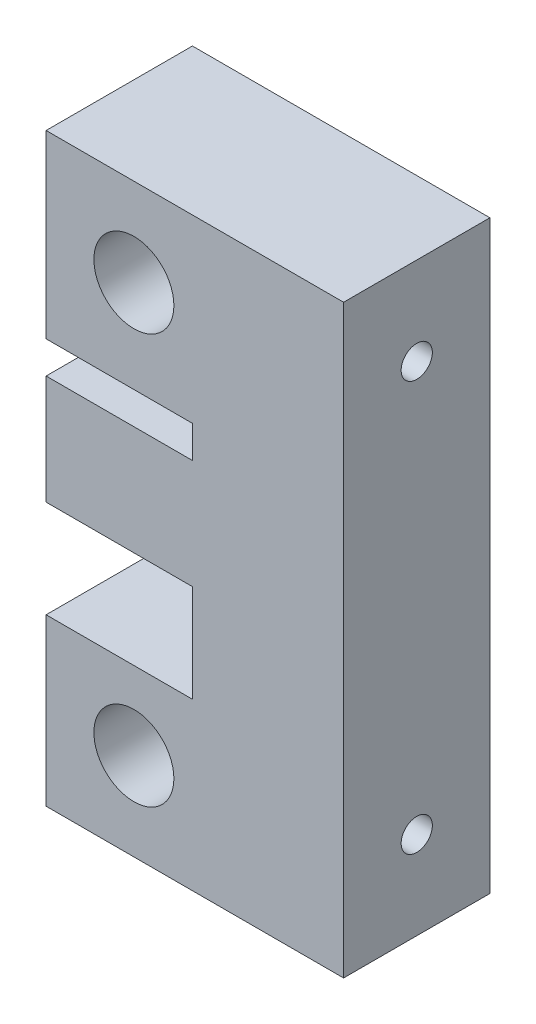
SolidWorks part; units mm, degrees
ref_plane "Front Plane" through (0, 0, 0) normal (0, 0, 1) x (1, 0, 0)
ref_plane "Top Plane" through (0, 0, 0) normal (0, 1, 0) x (1, 0, 0)
ref_plane "Right Plane" through (0, 0, 0) normal (1, 0, 0) x (0, 0, -1)
sketch "Sketch1" plane through (0, 0, 0) normal (0, 1, 0) x (1, 0, 0)
  line L1 (-15.25, 7.5) -> (15.25, 7.5)
  line L2 (-15.25, 7.5) -> (-15.25, -7.5)
  line L3 (-15.25, -7.5) -> (15.25, -7.5)
  line L4 (15.25, 7.5) -> (15.25, -7.5)
  point P4 (0, 7.5)
  point P6 (15.25, 0)
  dimension "D1" = 15
  dimension "D2" = 30.5
extrude "Boss-Extrude1" add sketch "Sketch1" along normal blind 60
sketch "Sketch2" plane through (0, 0, 7.5) normal (0, 0, 1) x (1, 0, 0)
  line L2 (-15.25, 0) -> (15.25, 0) construction
  line L4 (-15.25, 60) -> (-15.25, 0) construction
  circle A0 centre (-6.25, 51) radius 4.1
  circle A1 centre (-6.25, 9) radius 4.1
  dimension "D1" = 9
  dimension "D2" = 42
  dimension "D3" = 9
  dimension "D4" = 9
extrude "Cut-Extrude1" cut sketch "Sketch2" against normal through all
sketch "Sketch4" plane through (0, 0, 7.5) normal (0, 0, 1) x (1, 0, 0)
  line L0 (-15.25, 60) -> (-15.25, 0) construction
  line L1 (-15.25, 41.5) -> (-0.25, 41.5)
  line L2 (-15.25, 41.5) -> (-15.25, 38.2)
  line L3 (-15.25, 38.2) -> (-0.25, 38.2)
  line L4 (-0.25, 41.5) -> (-0.25, 38.2)
  line L5 (-15.25, 60) -> (15.25, 60) construction
  dimension "D1" = 15
  dimension "D2" = 18.5
  dimension "D3" = 3.3
extrude "Cut-Extrude2" cut sketch "Sketch4" against normal through all
sketch "Sketch5" plane through (0, 0, 7.5) normal (0, 0, 1) x (1, 0, 0)
  line L0 (-15.25, 38.2) -> (-15.25, 0) construction
  line L1 (-15.25, 17) -> (-0.25, 17)
  line L2 (-15.25, 17) -> (-15.25, 27)
  line L3 (-15.25, 27) -> (-0.25, 27)
  line L4 (-0.25, 17) -> (-0.25, 27)
  line L5 (-15.25, 0) -> (15.25, 0) construction
  dimension "D1" = 17
  dimension "D2" = 10
  dimension "D3" = 15
extrude "Cut-Extrude3" cut sketch "Sketch5" against normal through all
sketch "Sketch6" plane through (15.25, 0, 0) normal (1, 0, 0) x (0, 0, -1)
  line L0 (-7.5, 0) -> (7.5, 0) construction
  line L1 (-7.5, 60) -> (7.5, 60) construction
  line L2 (-7.5, 60) -> (-7.5, 0) construction
  circle A0 centre (0, 51) radius 1.6
  circle A1 centre (0, 9) radius 1.6
  dimension "D1" = 9
  dimension "D2" = 9
  dimension "D3" = 7.5
  dimension "D4" = 7.5
extrude "Cut-Extrude4" cut sketch "Sketch6" against normal blind 15
